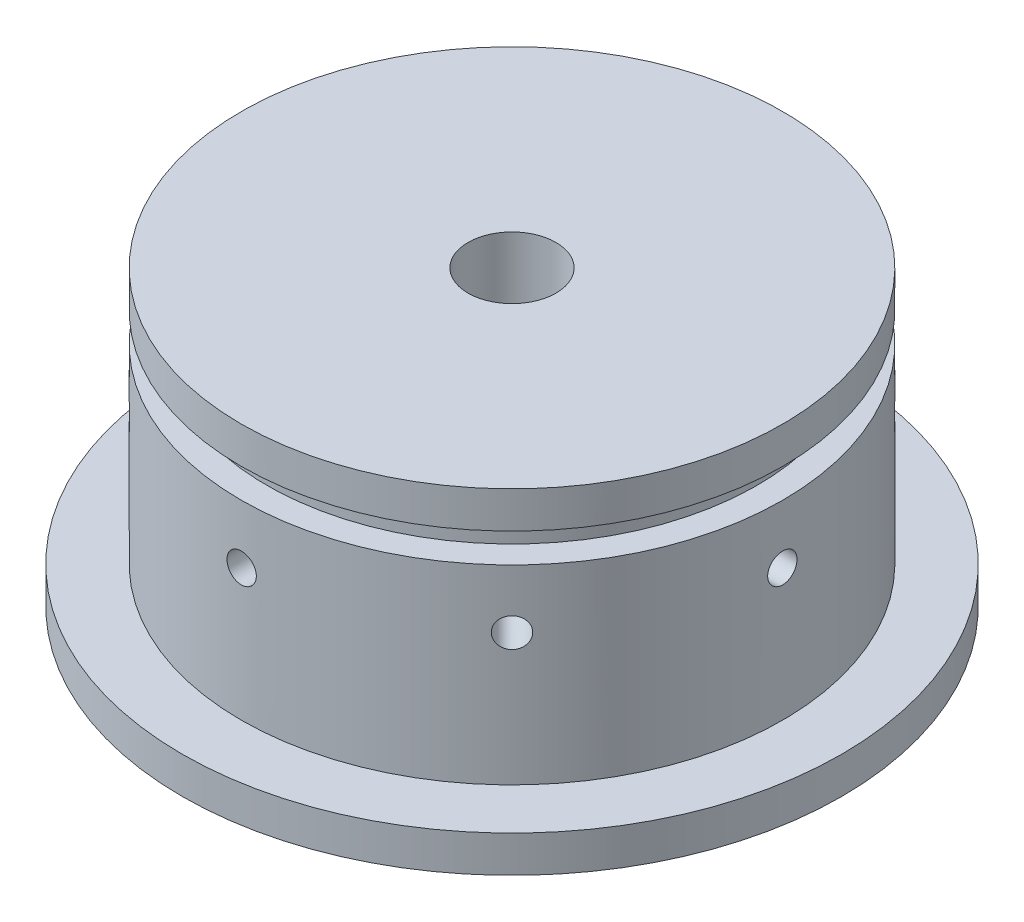
SolidWorks part; units mm, degrees
material "Delrin 2700 NC010, Low Viscosity Acetal Copolymer (SS)"
ref_plane "Front Plane" through (0, 0, 0) normal (0, 0, 1) x (1, 0, 0)
ref_plane "Top Plane" through (0, 0, 0) normal (0, 1, 0) x (1, 0, 0)
ref_plane "Right Plane" through (0, 0, 0) normal (1, 0, 0) x (0, 0, -1)
sketch "Sketch1" plane through (0, 0, 0) normal (0, 1, 0) x (1, 0, 0)
  circle A0 centre (0, 0) radius 45
extrude "Boss-Extrude1" add sketch "Sketch1" along normal blind 40
sketch "Sketch2" plane through (0, 40, 0) normal (0, 1, 0) x (1, 0, 0)
  circle A1 centre (0, 0) radius 36.95
  circle A2 centre (0, 0) radius 45
  dimension "D1" = 90
  dimension "D2" = 73.9
extrude "Cut-Extrude1" cut sketch "Sketch2" against normal blind 35
sketch "Sketch5" plane through (0, 0, 0) normal (0, 0, 1) x (1, 0, 0)
  line L0 (-36.95, 40) -> (-36.95, 35)
  line L1 (-36.95, 40) -> (-36.95, 5) construction
  line L2 (-36.95, 35) -> (-33.45, 35)
  line L3 (-33.45, 35) -> (-33.45, 31)
  line L4 (-33.45, 31) -> (-36.95, 31)
  line L5 (-36.95, 31) -> (-36.95, 35)
  line L6 (0, 0) -> (0, 24.8295)
  dimension "D1" = 5
  dimension "D2" = 4
  dimension "D4" = 3.5
revolve "Cut-Revolve1" cut sketch "Sketch5" angle 360 about L6
sketch "Sketch6" plane through (0, 0, 0) normal (0, 0, 1) x (1, 0, 0)
  line L0 (0, 23) -> (0, 5)
  line L1 (36.95, 5) -> (-36.95, 5) construction
  circle A0 centre (0, 23) radius 2
  dimension "D1" = 18
extrude "Cut-Extrude4" cut sketch "Sketch6" against normal blind 46 contours A0
sketch "Sketch8" plane through (0, 0, 0) normal (0, 0, -1) x (-1, 0, 0)
  circle A0 centre (0, 23) radius 2
extrude "Boss-Extrude2" add sketch "Sketch8" along normal blind 30
pattern_circular "CirPattern1" count 8 every 45 about axis through (0, 0, 0) along (0, 1, 0) of "Cut-Extrude4", "Boss-Extrude2"
sketch "Sketch4" plane through (0, 0, 0) normal (0, -1, 0) x (1, 0, 0)
  circle A0 centre (0, 0) radius 6
extrude "Cut-Extrude3" cut sketch "Sketch4" against normal blind 77
